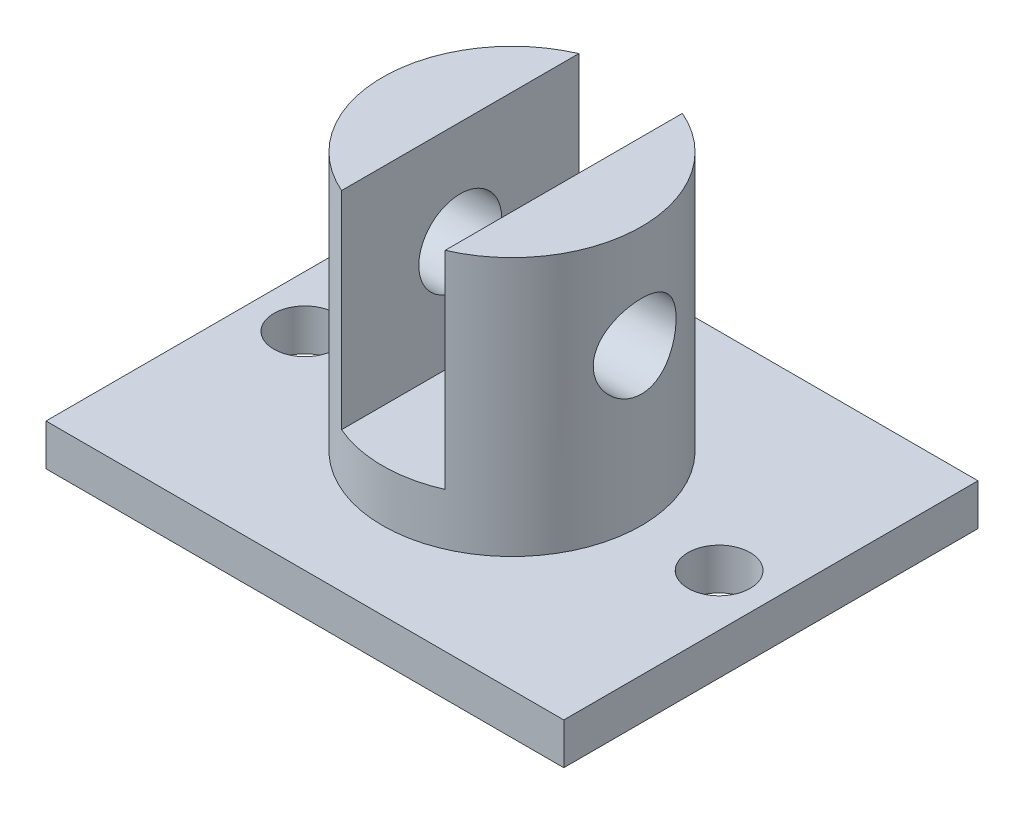
SolidWorks part; units mm, degrees
ref_plane "前视基准面" through (0, 0, 0) normal (0, 0, 1) x (1, 0, 0)
ref_plane "上视基准面" through (0, 0, 0) normal (0, 1, 0) x (1, 0, 0)
ref_plane "右视基准面" through (0, 0, 0) normal (1, 0, 0) x (0, 0, -1)
sketch "草图1" plane through (0, 0, 0) normal (0, 1, 0) x (1, 0, 0)
  line L1 (-25, 20) -> (25, 20)
  line L2 (-25, 20) -> (-25, -20)
  line L3 (-25, -20) -> (25, -20)
  line L4 (25, 20) -> (25, -20)
  line L5 (-25, 20) -> (25, -20) construction
  line L6 (-25, -20) -> (25, 20) construction
  point P0 (0, 0)
  dimension "D1" = 50
  dimension "D2" = 40
extrude "凸台-拉伸1" add sketch "草图1" along normal blind 4
sketch "草图2" plane through (0, 4, 0) normal (0, 1, 0) x (1, 0, 0)
  circle A0 centre (0, 0) radius 12.5
  dimension "D1" = 25
extrude "凸台-拉伸2" add sketch "草图2" along normal blind 25
sketch "草图3" plane through (0, 0, 0) normal (0, 0, 1) x (1, 0, 0)
  line L0 (12.5, 29) -> (-12.5, 29) construction
  line L1 (-5, 29) -> (5, 29)
  line L2 (-5, 29) -> (-5, 9)
  line L3 (-5, 9) -> (5, 9)
  line L4 (5, 29) -> (5, 9)
  line L5 (-5, 29) -> (5, 9) construction
  line L6 (-5, 9) -> (5, 29) construction
  point P0 (0, 19)
  dimension "D1" = 10
  dimension "D2" = 20
extrude "切除-拉伸1" cut sketch "草图3" against normal mid plane 40
sketch "草图4" plane through (0, 0, 0) normal (1, 0, 0) x (0, 0, -1)
  line L0 (11.4564, 29) -> (-11.4564, 29) construction
  circle A0 centre (0, 19) radius 4
  dimension "D1" = 8
  dimension "D2" = 10
extrude "切除-拉伸2" cut sketch "草图4" against normal through all both and the other way through all
sketch "草图5" plane through (0, 4, 0) normal (0, 1, 0) x (1, 0, 0)
  line L3 (20, -20) -> (20, 20)
  line L4 (20, -20) -> (20, 20) construction
  line L5 (-21, 0) -> (21, 0) construction
  line L6 (-20, 20) -> (-20, -20)
  line L7 (-20, 20) -> (-20, -20) construction
  circle A0 centre (-20, 0) radius 3
  circle A1 centre (20, 0) radius 3
  dimension "D3" = 6
  dimension "D4" = 6
  dimension "D1" = 5
  dimension "D2" = 5
extrude "切除-拉伸3" cut sketch "草图5" against normal blind 10
